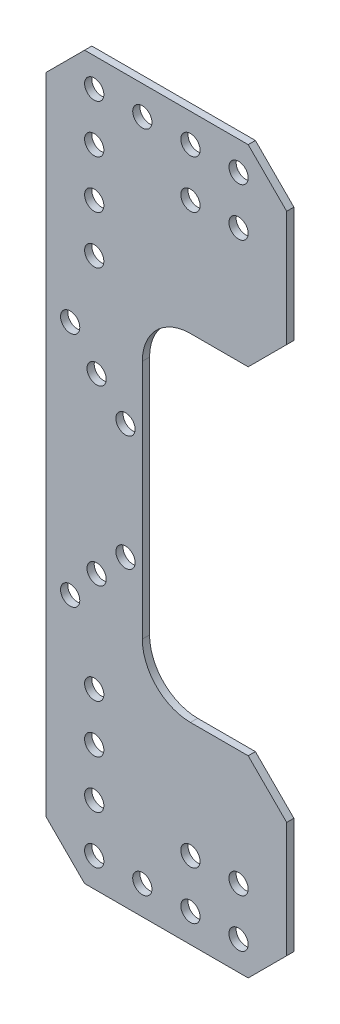
SolidWorks part; units mm, degrees
material "1060 Alloy"
ref_plane "Front Plane" through (0, 0, 0) normal (0, 0, 1) x (1, 0, 0)
ref_plane "Top Plane" through (0, 0, 0) normal (0, 1, 0) x (1, 0, 0)
ref_plane "Right Plane" through (0, 0, 0) normal (1, 0, 0) x (0, 0, -1)
sketch "Sketch1" plane through (0, 0, 0) normal (0, 0, 1) x (1, 0, 0)
  line L0 (-5.5, 35) -> (-5.5, -35)
  line L1 (0, 0) -> (-5.5, 0) construction
  line L2 (-5.5, 35) -> (-25.5, 35)
  line L3 (-25.5, 35) -> (-25.5, -35)
  line L4 (-25.5, -35) -> (-5.5, -35)
  line L5 (-20.5, -35) -> (-20.5, 35) construction
  circle A0 centre (0, 0) radius 30 construction
  circle A1 centre (-9, -12) radius 2
  circle A2 centre (-9, 12) radius 2
  circle A3 centre (-15, -18) radius 2
  circle A4 centre (-15, 18) radius 2
  circle A5 centre (-20.5, -24.5713) radius 2
  circle A6 centre (-20.5, 24.5713) radius 2
  dimension "D1" = 60
  dimension "D2" = 4
  dimension "D14" = 4
  dimension "D3" = 9
  dimension "D4" = 12
  dimension "D5" = 12
  dimension "D6" = 5.5
  dimension "D7" = 20
  dimension "D8" = 70
  dimension "D9" = 15
  dimension "D10" = 18
  dimension "D11" = 18
  dimension "D12" = 15
  dimension "D13" = 5
extrude "Boss-Extrude1" add sketch "Sketch1" along normal blind 1.5
sketch "Sketch2" plane through (0, 0, 1.5) normal (0, 0, 1) x (1, 0, 0)
  line L0 (-25.5, -35) -> (24.5, -35)
  line L1 (-25.5, 35) -> (-25.5, -35) construction
  line L2 (-25.5, -35) -> (-5.5, -35) construction
  line L3 (24.5, -35) -> (24.5, -75)
  line L4 (24.5, -75) -> (-25.5, -75)
  line L5 (-25.5, -75) -> (-25.5, -35)
  dimension "D1" = 40
  dimension "D2" = 50
extrude "Boss-Extrude2" add sketch "Sketch2" against normal up to surface (1.5 mm away) up to face at (-18.5, -24.5713, 0)
sketch "Sketch3" plane through (0, 0, 1.5) normal (0, 0, 1) x (1, 0, 0)
  line L0 (24.5, -69) -> (-25.5, -69) construction
  line L1 (24.5, -75) -> (24.5, -35) construction
  line L2 (-25.5, 35) -> (-25.5, -75) construction
  line L3 (-25.5, -75) -> (24.5, -75) construction
  line L4 (14.5, -59) -> (4.5, -59) construction
  line L5 (14.5, -59) -> (14.5, -69) construction
  line L6 (14.5, -69) -> (4.5, -59) construction
  line L7 (4.5, -59) -> (4.5, -69) construction
  circle A0 centre (14.5, -69) radius 2
  circle A1 centre (4.5, -69) radius 2
  circle A2 centre (-5.5, -69) radius 2
  circle A3 centre (-15.5, -69) radius 2
  circle A4 centre (4.5, -59) radius 2
  circle A5 centre (14.5, -59) radius 2
  circle A6 centre (-15.5, -59) radius 2
  circle A7 centre (-15.5, -49) radius 2
  circle A8 centre (-15.5, -39) radius 2
  dimension "D1" = 4
  dimension "D2" = 4
  dimension "D3" = 4
  dimension "D8" = 4
  dimension "D10" = 4
  dimension "D11" = 4
  dimension "D15" = 4
  dimension "D16" = 4
  dimension "D20" = 4
  dimension "D4" = 10
  dimension "D5" = 20
  dimension "D6" = 30
  dimension "D7" = 40
  dimension "D9" = 6
  dimension "D12" = 10
  dimension "D13" = 10
  dimension "D14" = 10
  dimension "D17" = 10
  dimension "D18" = 10
  dimension "D19" = 10
extrude "Cut-Extrude1" cut sketch "Sketch3" against normal blind 10
mirror "Mirror1" about plane through (0, 0, 0) normal (0, 1, 0) of "Cut-Extrude1", "Boss-Extrude2"
chamfer "Chamfer1" distance 8 angle 45 6 edges at (24.5, 75, 0.75) (-25.5, 75, 0.75) (-25.5, -75, 0.75) (24.5, -75, 0.75) (24.5, -35, 0.75) (24.5, 35, 0.75)
fillet "Fillet1" radius 10 2 edges at (-5.5, -35, 0.75) (-5.5, 35, 0.75)
